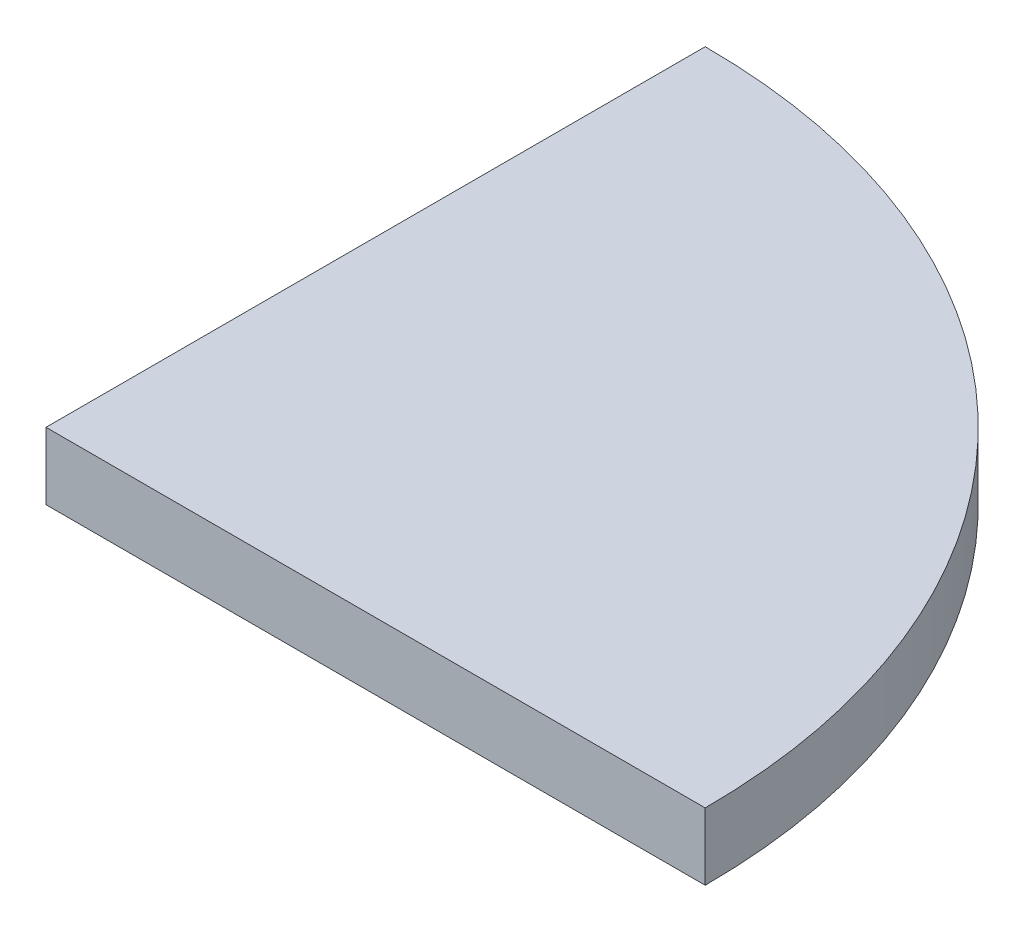
SolidWorks part; units mm, degrees
ref_plane "Front Plane" through (0, 0, 0) normal (0, 0, 1) x (1, 0, 0)
ref_plane "Top Plane" through (0, 0, 0) normal (0, 1, 0) x (1, 0, 0)
ref_plane "Right Plane" through (0, 0, 0) normal (1, 0, 0) x (0, 0, -1)
sketch "Sketch1" plane through (0, 0, 0) normal (0, 1, 0) x (1, 0, 0)
  line L0 (0, 0) -> (14.75, 0)
  line L1 (0, 14.75) -> (0, 0)
  arc A0 (14.75, 0) -> (0, 14.75) centre (0, 0) ccw
  dimension "D1" = 29.5
extrude "Boss-Extrude1" add sketch "Sketch1" along normal blind 1.5
